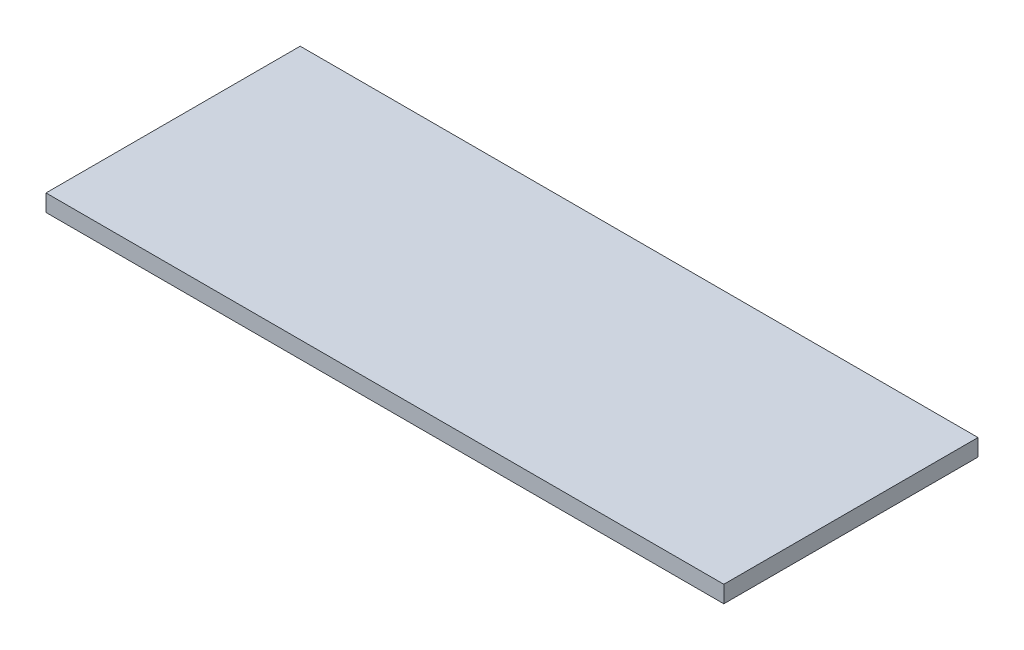
SolidWorks part; units mm, degrees
ref_plane "Front Plane" through (0, 0, 0) normal (0, 0, 1) x (1, 0, 0)
ref_plane "Top Plane" through (0, 0, 0) normal (0, 1, 0) x (1, 0, 0)
ref_plane "Right Plane" through (0, 0, 0) normal (1, 0, 0) x (0, 0, -1)
sketch "Sketch1" plane through (0, 0, 0) normal (0, 1, 0) x (1, 0, 0)
  line L1 (4000, 1500) -> (-4000, 1500)
  line L2 (4000, 1500) -> (4000, -1500)
  line L3 (4000, -1500) -> (-4000, -1500)
  line L4 (-4000, 1500) -> (-4000, -1500)
  line L5 (4000, 1500) -> (-4000, -1500) construction
  line L6 (4000, -1500) -> (-4000, 1500) construction
  point P0 (0, 0)
  dimension "D1" = 8000
  dimension "D2" = 3000
extrude "Boss-Extrude1" add sketch "Sketch1" along normal mid plane 200
